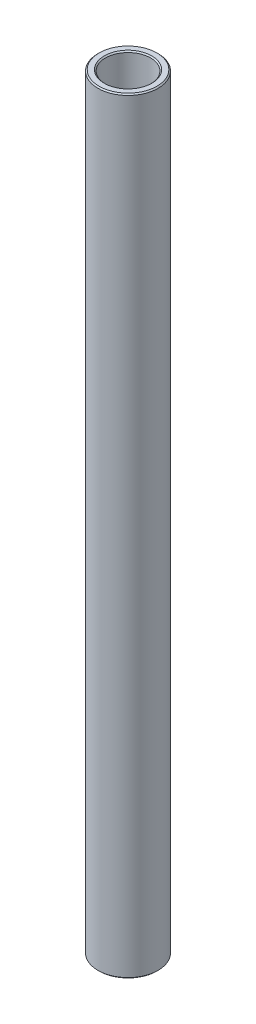
SolidWorks part; units mm, degrees
ref_plane "Front Plane" through (0, 0, 0) normal (0, 0, 1) x (1, 0, 0)
ref_plane "Top Plane" through (0, 0, 0) normal (0, 1, 0) x (1, 0, 0)
ref_plane "Right Plane" through (0, 0, 0) normal (1, 0, 0) x (0, 0, -1)
sketch "Sketch1" plane through (0, 0, 0) normal (0, 0, 1) x (1, 0, 0)
  line L0 (4.7625, 70.6437) -> (4.7625, 232.381)
  line L1 (4.7625, 232.381) -> (6.35, 232.381)
  line L2 (6.35, 232.381) -> (6.35, 70.6437)
  line L3 (6.35, 70.6437) -> (4.7625, 70.6437)
  line L4 (-10.0875, 79.3749) -> (-120.0875, 79.3749) construction
  line L6 (0, 61.1187) -> (0, 241.906) construction
  dimension "D1" = 9.525
  dimension "D2" = 9.525
  dimension "D3" = 12.7
  dimension "D4" = 9.525
revolve "Revolve1" add sketch "Sketch1" angle 360 about L6
chamfer "Chamfer1" distance 0.254 angle 45 4 edges at (6.35, 232.381, 0) (4.7625, 232.381, 0) (4.7625, 70.6437, 0) (6.35, 70.6437, 0)
equation "\"D4@Sketch1\"=\"D1@Sketch1\""
